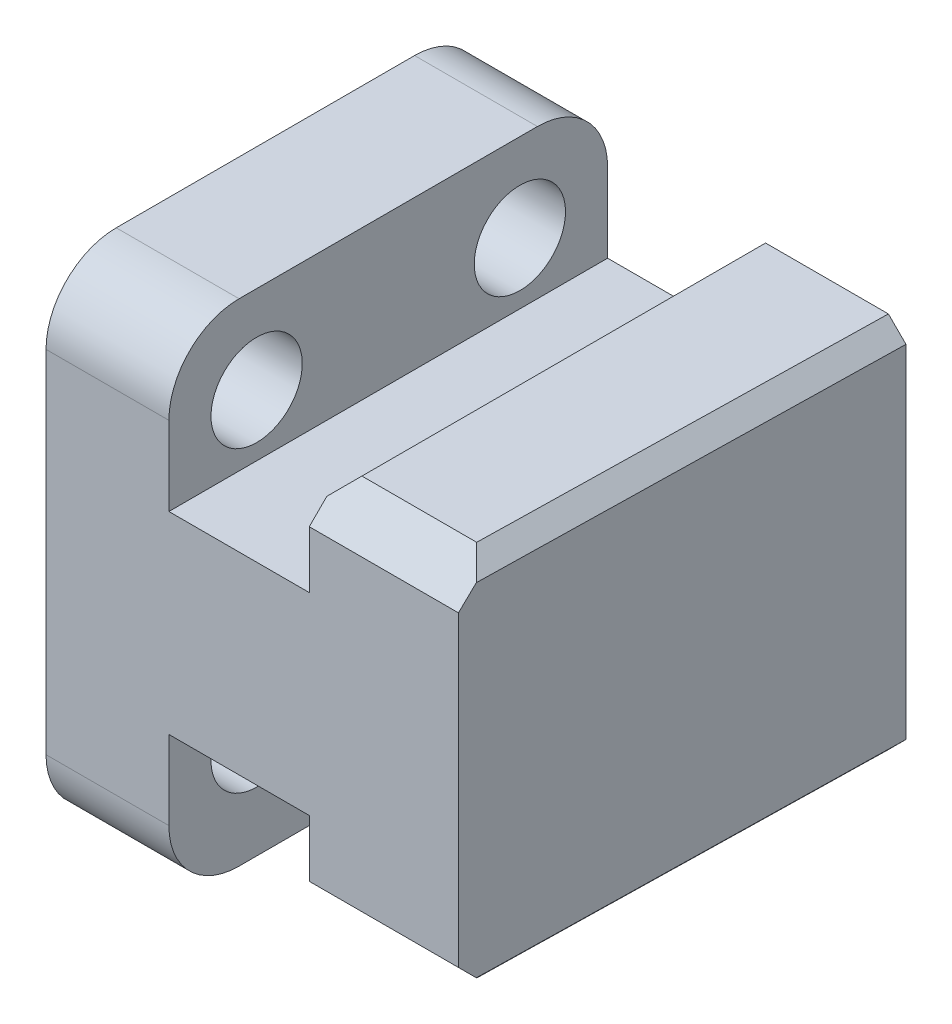
SolidWorks part; units mm, degrees
ref_plane "Front Plane" through (0, 0, 0) normal (0, 0, 1) x (1, 0, 0)
ref_plane "Top Plane" through (0, 0, 0) normal (0, 1, 0) x (1, 0, 0)
ref_plane "Right Plane" through (0, 0, 0) normal (1, 0, 0) x (0, 0, -1)
sketch "Sketch1" plane through (0, 0, 0) normal (0, 0, 1) x (1, 0, 0)
  line L0 (0, 14) -> (0, -14)
  line L1 (0, -14) -> (7, -14)
  line L2 (7, -14) -> (7, -5.5)
  line L3 (7, -5.5) -> (15, -5.5)
  line L4 (15, -5.5) -> (15, -10.75)
  line L5 (15, -10.75) -> (24, -10.75)
  line L6 (24, -10.75) -> (24, 10.75)
  line L7 (24, 10.75) -> (15, 10.75)
  line L8 (15, 10.75) -> (15, 5.5)
  line L9 (15, 5.5) -> (7, 5.5)
  line L10 (7, 5.5) -> (7, 14)
  line L11 (7, 14) -> (0, 14)
  dimension "D1" = 28
  dimension "D2" = 7
  dimension "D3" = 8
  dimension "D4" = 9
  dimension "D5" = 21.5
  dimension "D6" = 11
extrude "Boss-Extrude1" add sketch "Sketch1" along normal blind 25
sketch "Sketch2" plane through (0, 0, 0) normal (-1, 0, 0) x (0, 0, 1)
  line L0 (25, 14) -> (0, 14) construction
  line L1 (25, 14) -> (25, -14) construction
  line L2 (0, 14) -> (0, -14) construction
  line L3 (25, -14) -> (0, -14) construction
  circle A0 centre (5, 9) radius 2.6
  circle A1 centre (20, 9) radius 2.6
  circle A2 centre (5, -8) radius 2.6
  circle A3 centre (20, -8) radius 2.6
  dimension "D2" = 5.2
  dimension "D1" = 5
  dimension "D3" = 5
  dimension "D4" = 5
  dimension "D5" = 6
extrude "Cut-Extrude1" cut sketch "Sketch2" against normal blind 8
sketch "Sketch3" plane through (0, 10.75, 0) normal (0, 1, 0) x (1, 0, 0)
  line L0 (24, 0) -> (23.5, -25)
  line L1 (24, -25) -> (15, -25) construction
  line L2 (23.5, -25) -> (24, -25)
  line L3 (24, -25) -> (24, 0)
  dimension "D1" = 0.5
extrude "Cut-Extrude2" cut sketch "Sketch3" against normal through all
fillet "Fillet1" radius 4 4 edges at (3.5, 14, 0) (3.5, -14, 0) (3.5, -14, 25) (3.5, 14, 25)
chamfer "Chamfer1" distance 2 angle 45 2 edges at (19.25, -10.75, 25) (19.25, 10.75, 25)
chamfer "Chamfer2" distance 1 angle 45 4 edges at (15, -10.75, 11.5) (15, 10.75, 11.5) (23.77, -10.75, 11.5) (23.77, 10.75, 11.5)
